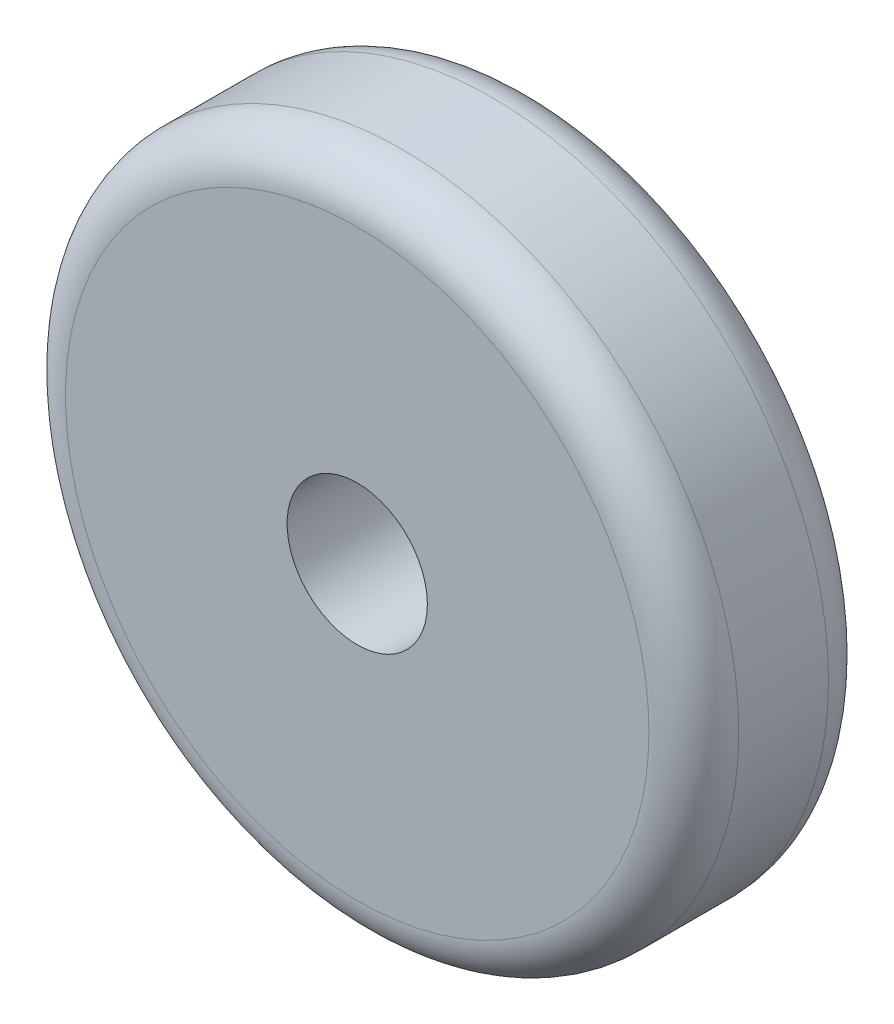
SolidWorks part; units mm, degrees
ref_plane "Front Plane" through (0, 0, 0) normal (0, 0, 1) x (1, 0, 0)
ref_plane "Top Plane" through (0, 0, 0) normal (0, 1, 0) x (1, 0, 0)
ref_plane "Right Plane" through (0, 0, 0) normal (1, 0, 0) x (0, 0, -1)
sketch "Sketch2" plane through (0, 0, 0) normal (0, 0, 1) x (1, 0, 0)
  circle A0 centre (0, 0) radius 19.05
  circle A1 centre (0, 0) radius 3.9688
  dimension "D1" = 38.1
  dimension "D2" = 7.9375
extrude "Boss-Extrude1" add sketch "Sketch2" along normal blind 10.16
fillet "Fillet1" radius 2.54 2 edges at (19.05, 0, 10.16) (19.05, 0, 0)
